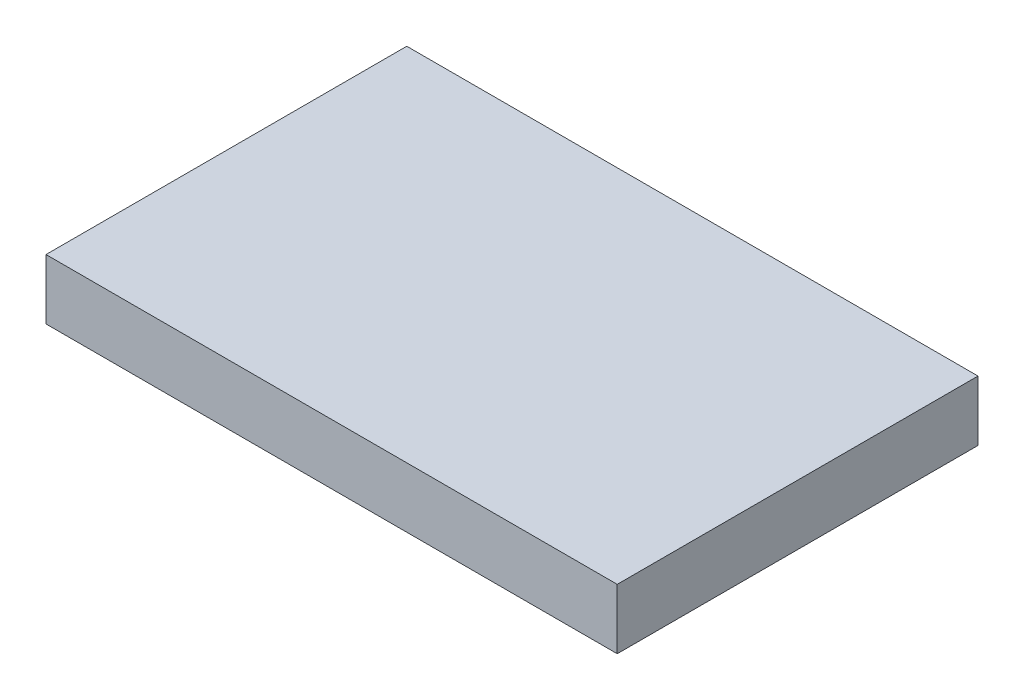
SolidWorks part; units mm, degrees
material "PVC Rigid"
ref_plane "Front Plane" through (0, 0, 0) normal (0, 0, 1) x (1, 0, 0)
ref_plane "Top Plane" through (0, 0, 0) normal (0, 1, 0) x (1, 0, 0)
ref_plane "Right Plane" through (0, 0, 0) normal (1, 0, 0) x (0, 0, -1)
sketch "Sketch1" plane through (0, 0, 0) normal (0, 1, 0) x (1, 0, 0)
  line L1 (0, 0) -> (90.4875, 0)
  line L2 (0, 0) -> (0, 57.15)
  line L3 (0, 57.15) -> (90.4875, 57.15)
  line L4 (90.4875, 0) -> (90.4875, 57.15)
  dimension "D1" = 90.4875
  dimension "D2" = 57.15
extrude "Boss-Extrude1" add sketch "Sketch1" along normal blind 9.525
